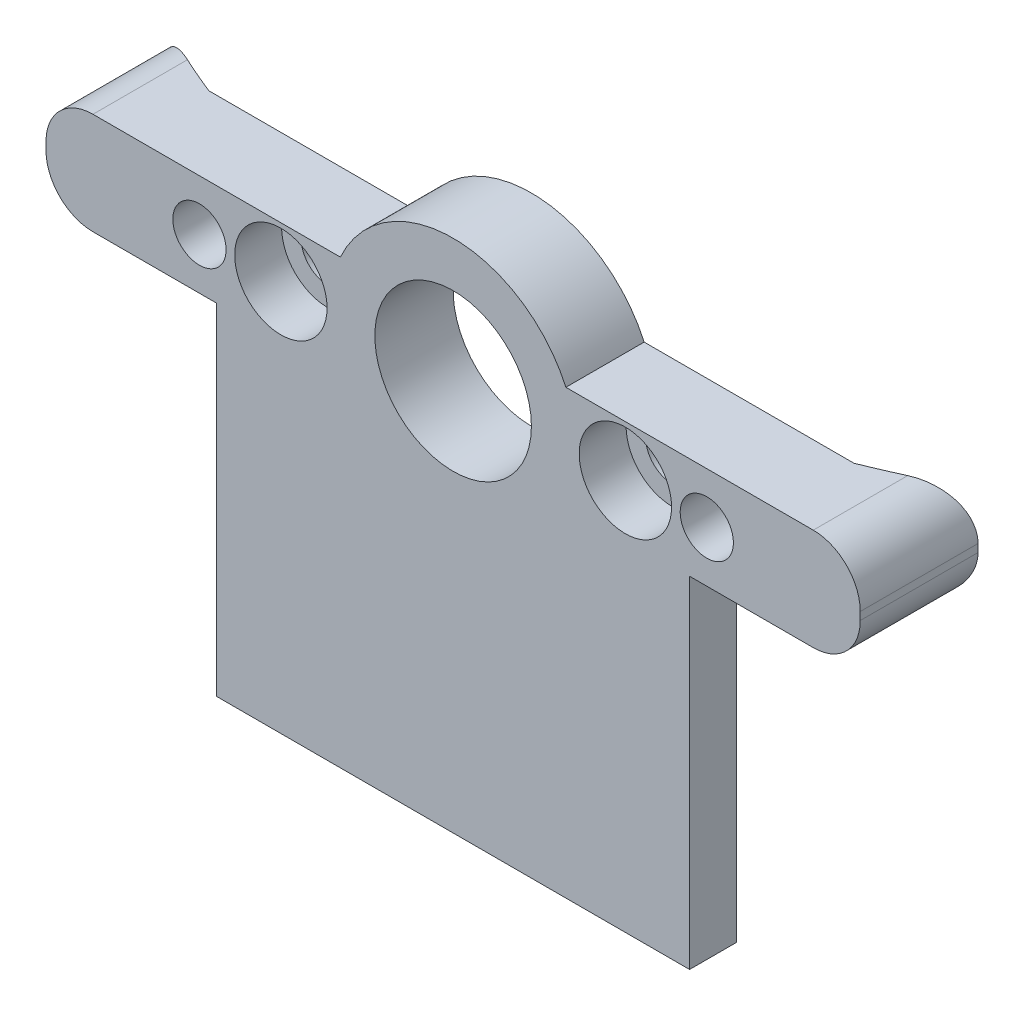
SolidWorks part; units mm, degrees
material "PLA"
ref_plane "Alzado" through (0, 0, 0) normal (0, 0, 1) x (1, 0, 0)
ref_plane "Planta" through (0, 0, 0) normal (0, 1, 0) x (1, 0, 0)
ref_plane "Vista lateral" through (0, 0, 0) normal (1, 0, 0) x (0, 0, -1)
sketch "Croquis1" plane through (0, 0, 0) normal (0, 0, 1) x (1, 0, 0)
  line L0 (-7.2005, 3.25) -> (-26, 3.25)
  line L1 (26, -3.25) -> (7.2005, -3.25)
  line L2 (26, -3.25) -> (26, 3.25)
  line L3 (26, 3.25) -> (7.2005, 3.25)
  line L4 (-26, -3.25) -> (-26, 3.25)
  line L5 (26, -3.25) -> (-26, 3.25) construction
  line L6 (26, 3.25) -> (-26, -3.25) construction
  line L9 (-7.2005, -3.25) -> (-26, -3.25)
  arc A0 (-7.2005, -3.25) -> (7.2005, -3.25) centre (0, 0) ccw
  circle A1 centre (0, 0) radius 5
  arc A2 (7.2005, 3.25) -> (-7.2005, 3.25) centre (0, 0) ccw
  dimension "D3" = 10
  dimension "D4" = 7.9
  dimension "D1" = 52
  dimension "D2" = 6.5
extrude "Saliente-Extruir1" add sketch "Croquis1" along normal blind 5
sketch "Croquis2" plane through (0, 0, 5) normal (0, 0, 1) x (1, 0, 0)
  line L0 (-11, 0) -> (11, 0) construction
  circle A0 centre (-11, 0) radius 1.7
  circle A1 centre (11, 0) radius 1.7
  point P2 (0, 0)
  dimension "D1" = 3.4
  dimension "D2" = 22
extrude "Cortar-Extruir1" cut sketch "Croquis2" against normal up to surface (5 mm away) up to face at (0, 0, 0)
sketch "Croquis3" plane through (0, 0, 5) normal (0, 0, 1) x (1, 0, 0)
  circle A0 centre (-11, 0) radius 2.95
  circle A1 centre (11, 0) radius 2.95
  dimension "D1" = 5.9
extrude "Cortar-Extruir2" cut sketch "Croquis3" against normal blind 3
sketch "Croquis4" plane through (0, 0, 0) normal (0, 1, 0) x (1, 0, 0)
  line L0 (-26, 0) -> (-20.6, 0)
  line L1 (-7.2005, 0) -> (-26, 0) construction
  line L2 (-26, 0) -> (-26, 2.52)
  arc A0 (-26, 2.52) -> (-20.6, 0) centre (-0.0755, 51.0269) ccw
  dimension "D1" = 55
  dimension "D2" = 2.52
  dimension "D3" = 5.4
extrude "Saliente-Extruir2" add sketch "Croquis4" along normal up to surface (3.25 mm away) and the other way up to surface (3.25 mm away) up to face at (-16.6003, 3.25, 2.5) other way up to face at (-16.6003, -3.25, 2.5)
sketch "Croquis5" plane through (0, 0, 5) normal (0, 0, 1) x (1, 0, 0)
  circle A0 centre (-16.2, 0) radius 1.7
  dimension "D2" = 3.4
  dimension "D1" = 16.2
extrude "Cortar-Extruir3" cut sketch "Croquis5" against normal blind 10
sketch "Croquis6" plane through (0, 0, 0) normal (0, 0, -1) x (-1, 0, 0)
  line L1 (19.55, 0) -> (17.875, 2.9012)
  line L2 (17.875, 2.9012) -> (14.525, 2.9012)
  line L3 (14.525, 2.9012) -> (12.85, 0)
  line L4 (12.85, 0) -> (14.525, -2.9012)
  line L5 (14.525, -2.9012) -> (17.875, -2.9012)
  line L6 (17.875, -2.9012) -> (19.55, 0)
  circle A0 centre (16.2, 0) radius 3.35 construction
  dimension "D1" = 3.35
extrude "Cortar-Extruir4" cut sketch "Croquis6" against normal blind 1.7 contours L4 L5 L6 L1 L2 L3
mirror "Simetría2" about plane through (0, 0, 0) normal (1, 0, 0) of "Cortar-Extruir4", "Cortar-Extruir3", "Saliente-Extruir2"
fillet "Redondeo1" radius 3 4 edges at (-26, -3.25, 1.24) (-26, 3.25, 1.24) (26, -3.25, 1.24) (26, 3.25, 1.24)
sketch "Croquis7" plane through (0, 0, 5) normal (0, 0, 1) x (1, 0, 0)
  line L0 (-23, -3.25) -> (-7.2005, -3.25) construction
  line L1 (-15.1003, -3.25) -> (-7.2005, -3.25)
  line L2 (-15.1003, -3.25) -> (-15.1003, -25)
  line L3 (-15.1003, -25) -> (15.1003, -25)
  line L4 (15.1003, -3.25) -> (15.1003, -25)
  line L5 (7.2005, -3.25) -> (23, -3.25) construction
  line L6 (7.2005, -3.25) -> (15.1003, -3.25)
  arc A1 (-7.2005, -3.25) -> (7.2005, -3.25) centre (0, 0) ccw construction
  arc A2 (-7.2005, -3.25) -> (7.2005, -3.25) centre (0, 0) ccw
  point P12 (0, -25)
  dimension "D1" = 25
extrude "Saliente-Extruir3" add sketch "Croquis7" against normal blind 2.5 contours L2 L3 L4 L6 A2 L1
sketch "Croquis8" plane through (0, -25, 0) normal (0, -1, 0) x (1, 0, 0)
  line L0 (-15.1003, 2.5) -> (-15.1003, 2)
  line L1 (-15.1003, 2.5) -> (-12.8003, 2.5)
  line L3 (0, 0) -> (0, 9.5214) construction
  line L4 (15.1003, 2.5) -> (12.8003, 2.5)
  line L5 (15.1003, 2.5) -> (15.1003, 2)
  arc A0 (-12.8003, 2.5) -> (-15.1003, 2) centre (-2.2693, -51.4824) ccw
  arc A1 (12.8003, 2.5) -> (15.1003, 2) centre (2.2693, -51.4824) cw
  dimension "D1" = 55
  dimension "D2" = 2.3
  dimension "D3" = 0.5
extrude "Saliente-Extruir4" add sketch "Croquis8" against normal up to surface (21.75 mm away) up to face at (-15.8868, -3.25, 1.9974)
